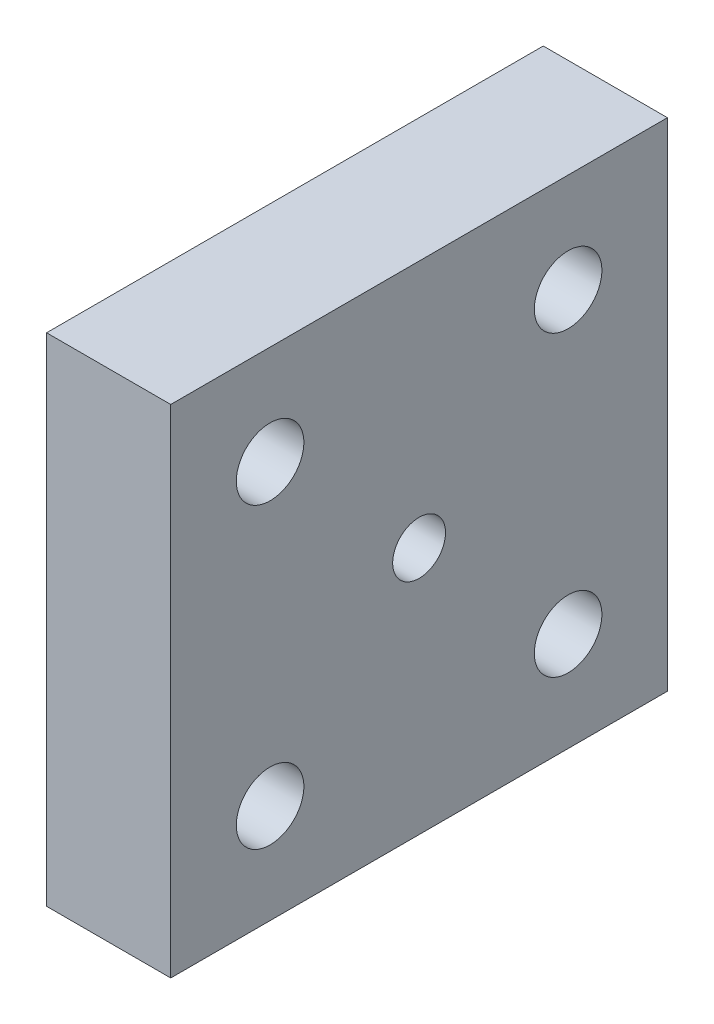
SolidWorks part; units mm, degrees
ref_plane "Front Plane" through (0, 0, 0) normal (0, 0, 1) x (1, 0, 0)
ref_plane "Top Plane" through (0, 0, 0) normal (0, 1, 0) x (1, 0, 0)
ref_plane "Right Plane" through (0, 0, 0) normal (1, 0, 0) x (0, 0, -1)
sketch "Sketch1" plane through (0, 0, 0) normal (1, 0, 0) x (0, 0, -1)
  line L1 (0, 0) -> (25.4, 0)
  line L2 (0, 0) -> (0, -25.4)
  line L3 (0, -25.4) -> (25.4, -25.4)
  line L4 (25.4, 0) -> (25.4, -25.4)
  point P5 (12.7, -12.7)
  point P6 (0, 0)
  point P8 (12.7, -25.4)
  point P9 (0, 0)
  point P10 (25.4, -12.7)
  point P15 (5.08, -5.08)
  point P18 (20.32, -5.08)
  point P19 (20.32, -20.32)
  point P20 (5.08, -20.32)
  dimension "D2" = 25.4
  dimension "D4" = 25.4
extrude "Boss-Extrude1" add sketch "Sketch1" along normal blind 6.35
sketch "Sketch6" plane through (0, 0, 0) normal (-1, 0, 0) x (0, 0, 1)
  line L0 (-25.4, -25.4) -> (-25.4, 0) construction
  line L1 (-25.4, 0) -> (0, 0) construction
  point P0 (-20.32, -20.32)
  point P1 (-20.32, -5.08)
  point P2 (-5.08, -5.08)
  point P3 (-5.08, -20.32)
  point P4 (-12.7, -12.7)
  point P5 (0, 0)
  point P8 (-25.4, -12.7)
  point P9 (0, 0)
  point P12 (-12.7, 0)
  point P13 (0, 0)
  point P14 (0, 0)
  point P15 (0, 0)
  point P16 (0, 0)
  dimension "D1" = 7.62
  dimension "D2" = 7.62
  dimension "D3" = 7.62
  dimension "D4" = 7.62
hole_wizard "#8-32 Tapped Hole5" positions "Sketch7" profile "Sketch9" tap size "#8-32" standard "ANSI Inch" end condition through all
sketch "Sketch7" plane through (0, 0, 0) normal (-1, 0, 0) x (0, 0, 1)
  point P0 (-20.32, -20.32)
  point P3 (-20.32, -5.08)
  point P6 (-5.08, -5.08)
  point P9 (-5.08, -20.32)
sketch "Sketch9" plane through (0, -20.32, -20.32) normal (0, 1, 0) x (0, 0, 1)
  line L0 (0, 0) -> (0, 6.35)
  line L1 (0, 6.35) -> (1.7272, 6.35)
  line L2 (1.7272, 6.35) -> (1.7272, 0)
  line L5 (1.7272, 0) -> (0, 0)
  line L11 (0, -6.35) -> (0, 107.95) construction
  dimension "Thru Tap Drill Dia." = 3.4544
  dimension "Thru Tap Drill Depth" = 6.35
cosmetic thread "Hole Thread1"
cosmetic thread "Hole Thread2"
cosmetic thread "Hole Thread3"
cosmetic thread "Hole Thread4"
hole_wizard "#6-32 Tapped Hole1" positions "Sketch10" profile "Sketch11" tap size "#6-32" standard "ANSI Inch" end condition through all
sketch "Sketch10" plane through (0, 0, 0) normal (-1, 0, 0) x (0, 0, 1)
  point P0 (-12.7, -12.7)
sketch "Sketch11" plane through (0, -12.7, -12.7) normal (0, 1, 0) x (0, 0, 1)
  line L0 (0, 0) -> (0, 6.35)
  line L1 (0, 6.35) -> (1.3525, 6.35)
  line L2 (1.3525, 6.35) -> (1.3525, 0)
  line L5 (1.3525, 0) -> (0, 0)
  line L11 (0, -6.35) -> (0, 107.95) construction
  dimension "Thru Tap Drill Dia." = 2.7051
  dimension "Thru Tap Drill Depth" = 6.35
cosmetic thread "Hole Thread5"
